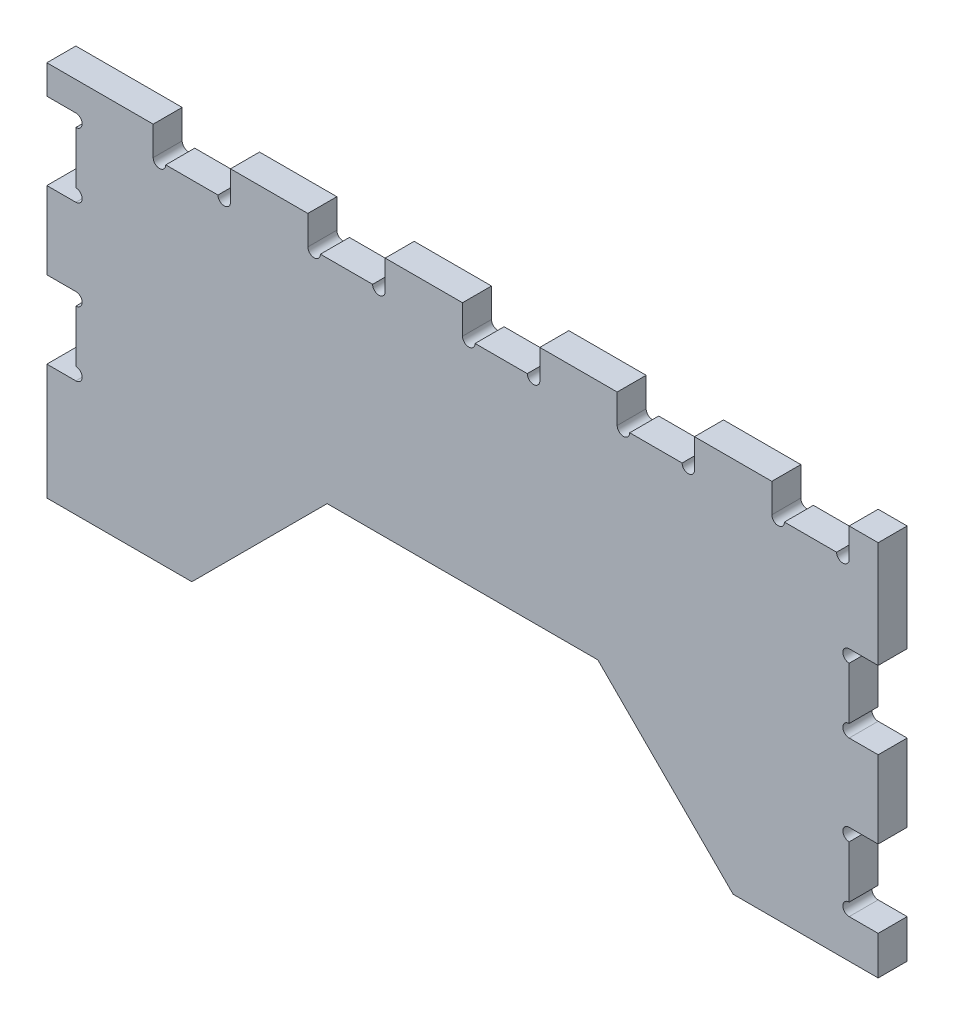
SolidWorks part; units mm, degrees
ref_plane "Alzado" through (0, 0, 0) normal (0, 0, 1) x (1, 0, 0)
ref_plane "Planta" through (0, 0, 0) normal (0, 1, 0) x (1, 0, 0)
ref_plane "Vista lateral" through (0, 0, 0) normal (1, 0, 0) x (0, 0, -1)
sketch "Croquis1" plane through (0, 0, 0) normal (0, 0, 1) x (1, 0, 0)
  line L0 (140, -90) -> (215, -90)
  line L1 (-215, 90) -> (215, 90)
  line L2 (-215, 90) -> (-215, -90)
  line L3 (-215, -90) -> (-140, -90)
  line L4 (215, 90) -> (215, -90)
  line L5 (-215, 90) -> (215, -90) construction
  line L6 (-215, -90) -> (215, 90) construction
  line L7 (140, -90) -> (215, -90)
  line L8 (-215, -90) -> (-140, -90)
  line L9 (-215, -90) -> (-215, -20)
  line L10 (-70, -20) -> (70, -20)
  line L11 (215, -90) -> (215, -20)
  line L12 (-215, -90) -> (-95, -90)
  line L13 (-215, -90) -> (-215, -20)
  line L14 (-215, -20) -> (-95, -20)
  line L17 (215, -90) -> (140, -90)
  line L18 (215, -90) -> (215, -20)
  line L19 (-95, -45) -> (-70, -20)
  line L20 (95, -45) -> (70, -20)
  line L21 (70, -20) -> (140, -90)
  line L22 (-70, -20) -> (-140, -90)
  point P0 (0, 0)
  dimension "D1" = 430
  dimension "D2" = 70
  dimension "75" = 180
  dimension "D3" = 120
extrude "Saliente-Extruir1" add sketch "Croquis1" along normal blind 15
sketch "Croquis2" plane through (0, 90, 0) normal (0, 1, 0) x (1, 0, 0)
  line L4 (215, 0) -> (-215, 0)
  line L5 (-215, 0) -> (-215, -15)
  line L6 (-215, -15) -> (215, -15)
  line L7 (215, -15) -> (215, 0)
  line L8 (215, 0) -> (-215, 0)
  line L9 (-215, 0) -> (-215, -15)
  line L10 (-215, -15) -> (215, -15)
  line L11 (215, -15) -> (215, 0)
  dimension "D1" = 0
extrude "Saliente-Extruir2" add sketch "Croquis2" along normal blind 15
sketch "Croquis3" plane through (0, 0, 15) normal (0, 0, 1) x (1, 0, 0)
  line L0 (0, 105) -> (0, 90)
  line L1 (0, -20) -> (0, 55.1066)
  line L3 (-215, 105) -> (-215, 90)
  line L5 (0, 105) -> (0, 90)
  line L7 (215, 105) -> (215, 90)
  line L8 (-140, -90) -> (-70, -20)
  line L9 (-70, -20) -> (70, -20)
  line L10 (70, -20) -> (140, -90)
  line L11 (140, -90) -> (215, -90)
  line L12 (215, -90) -> (215, 105)
  line L13 (215, 105) -> (-215, 105)
  line L14 (-215, 105) -> (-215, -90)
  line L15 (-215, -90) -> (-140, -90)
  line L17 (-70, -20) -> (70, -20)
  line L18 (70, -20) -> (140, -90)
  line L19 (140, -90) -> (215, -90)
  line L20 (215, -90) -> (215, 105)
  line L22 (-215, 105) -> (-215, -90)
  line L23 (-215, -90) -> (-140, -90)
  line L24 (193.5, 90) -> (166.5, 90)
  line L25 (0, 105) -> (0, 90)
  line L26 (193.5, 90) -> (166.5, 90)
  line L27 (0, 90) -> (0, 140.4543)
  line L30 (200, 90) -> (200, 124.6542)
  line L31 (40, 124.6542) -> (40, 90)
  line L35 (-160, 90) -> (-160, 105)
  line L36 (-160, 124.6542) -> (-120, 124.6542)
  line L37 (-160, 124.6542) -> (-160, 90)
  line L38 (-153.5, 90) -> (-126.5, 90)
  line L39 (-120, 124.6542) -> (-120, 90)
  line L41 (-120, 124.6542) -> (-120, 90)
  line L43 (-80, 124.6542) -> (-80, 90)
  line L44 (-73.5, 90) -> (-46.5, 90)
  line L45 (-80, 90) -> (-80, 124.6542)
  line L46 (-80, 124.6542) -> (-40, 124.6542)
  line L47 (-40, 90) -> (-40, 124.6542)
  line L48 (0, 124.6542) -> (40, 124.6542)
  line L49 (-40, 124.6542) -> (-40, 90)
  line L50 (6.5, 90) -> (33.5, 90)
  line L51 (0, 124.6542) -> (0, 90)
  line L52 (-153.5, 90) -> (-126.5, 90)
  line L53 (40, 90) -> (40, 124.6542)
  line L54 (113.6, 90) -> (86.5, 90)
  line L55 (80, 90) -> (80, 124.6542)
  line L56 (113.6, 90) -> (86.5, 90)
  line L57 (80, 124.6542) -> (80, 90)
  line L58 (120, 124.6542) -> (80, 124.6542)
  line L59 (120, 124.6542) -> (120, 90)
  line L60 (193.5, 90) -> (166.5, 90)
  line L61 (120, 124.6542) -> (120, 90)
  line L62 (-200, 105) -> (-215, 105)
  line L63 (160, 124.6542) -> (160, 90)
  line L64 (200, 124.6542) -> (160, 124.6542)
  line L65 (160, 90) -> (160, 124.6542)
  line L67 (200, 90) -> (200, 124.6542)
  line L76 (113.6, 90) -> (86.5, 90)
  line L82 (-126.5, 90) -> (-153.5, 90)
  line L83 (-73.5, 90) -> (-46.5, 90)
  line L85 (-46.5, 90) -> (-73.5, 90)
  line L89 (33.5, 90) -> (6.5, 90)
  line L90 (33.5, 90) -> (6.5, 90)
  arc A0 (-160, 90) -> (-153.5, 90) centre (-156.75, 90) ccw
  arc A1 (-126.5, 90) -> (-120, 90) centre (-123.25, 90) ccw
  arc A2 (-80, 90) -> (-73.5, 90) centre (-76.75, 90) ccw
  arc A3 (-46.5, 90) -> (-40, 90) centre (-43.25, 90) ccw
  arc A4 (0, 90) -> (6.5, 90) centre (3.25, 90) ccw
  arc A5 (33.5, 90) -> (40, 90) centre (36.75, 90) ccw
  arc A6 (80, 90) -> (86.5, 90) centre (83.25, 90) ccw
  arc A7 (113.6, 90) -> (120, 90) centre (116.8, 90) ccw
  arc A8 (160, 90) -> (166.5, 90) centre (163.25, 90) ccw
  arc A9 (193.5, 90) -> (200, 90) centre (196.75, 90) ccw
  line M48 (215, 105) -> (-215, 105)
  dimension "D2" = 15
  dimension "D3" = 3.25
  dimension "D4" = 3.25
  dimension "D5" = 40
  dimension "D6" = 40
  dimension "D7" = 40
  dimension "D8" = 3.25
  dimension "D9" = 3.25
  dimension "D10" = 3.25
  dimension "D11" = 3.25
  dimension "D12" = 3.25
  dimension "D13" = 3.2
  dimension "D14" = 3.25
  dimension "D15" = 3.25
  dimension "D1" = 0
extrude "Cortar-Extruir2" cut sketch "Croquis3" against normal blind 15 contours L39 L36 L37 M48 | L38 A1 L39 L35 A0 M48 | L44 A3 L47 L43 A2 M48 | L47 L46 L43 M48 | L50 A5 L31 L0 A4 M48 | L48 L27 L31 M48 | L24 A9 L30 L63 A8 M48 | L30 L64 L63 M48 | L59 L58 L55 M48 | L54 A7 L59 L55 A6 M48
sketch "Croquis4" plane through (0, 0, 15) normal (0, 0, 1) x (1, 0, 0)
  line L0 (-215, 10) -> (-215, -90)
  line L2 (-215, 105) -> (-215, 50)
  line L3 (-215, -90) -> (-200, -90)
  line L4 (-200, 83.5) -> (-200, 56.5)
  line L6 (-215, 105) -> (-215, 90)
  line L7 (-215, 90) -> (-200, 90)
  line L9 (-215, 90) -> (-200, 90)
  line L10 (-215, 90) -> (-215, 50)
  line L11 (-215, 50) -> (-200, 50)
  line L12 (-200, 83.5) -> (-200, 56.5)
  line L13 (-215, 50) -> (-200, 50)
  line L15 (-215, 10) -> (-200, 10)
  line L17 (-215, 10) -> (-200, 10)
  line L18 (-215, 10) -> (-215, -30)
  line L19 (-215, -30) -> (-200, -30)
  line L21 (-200, 50) -> (-200, 53.25)
  line L24 (-200, 53.25) -> (-200, 50)
  line L25 (-200, 53.25) -> (-200, 50)
  line L26 (-200, 3.5) -> (-200, -23.5)
  line L27 (-200, 3.5) -> (-200, -23.5)
  line L28 (-80, 105) -> (-120, 105)
  line L29 (-120, 105) -> (-120, 90)
  line L30 (-126.5, 90) -> (-153.5, 90)
  line L31 (-160, 90) -> (-160, 105)
  line L32 (-160, 105) -> (-215, 105)
  line L33 (-215, 105) -> (-215, -90)
  line L34 (-215, -90) -> (-140, -90)
  line L35 (-140, -90) -> (-70, -20)
  line L36 (-70, -20) -> (70, -20)
  line L37 (70, -20) -> (140, -90)
  line L38 (140, -90) -> (215, -90)
  line L39 (215, -90) -> (215, 105)
  line L40 (215, 105) -> (200, 105)
  line L41 (200, 105) -> (200, 90)
  line L42 (193.5, 90) -> (166.5, 90)
  line L43 (160, 90) -> (160, 105)
  line L44 (160, 105) -> (120, 105)
  line L45 (120, 105) -> (120, 90)
  line L46 (113.6, 90) -> (86.5, 90)
  line L47 (80, 90) -> (80, 105)
  line L48 (80, 105) -> (40, 105)
  line L49 (40, 105) -> (40, 90)
  line L50 (33.5, 90) -> (6.5, 90)
  line L51 (0, 90) -> (0, 105)
  line L52 (0, 105) -> (-40, 105)
  line L53 (-40, 105) -> (-40, 90)
  line L54 (-46.5, 90) -> (-73.5, 90)
  line L55 (-80, 90) -> (-80, 105)
  line L56 (-80, 105) -> (-120, 105)
  line L57 (-120, 105) -> (-120, 90)
  line L58 (-126.5, 90) -> (-153.5, 90)
  line L59 (-160, 90) -> (-160, 105)
  line L61 (-215, 105) -> (-215, -90)
  line L62 (-215, -90) -> (-140, -90)
  line L63 (-140, -90) -> (-70, -20)
  line L64 (-70, -20) -> (70, -20)
  line L65 (70, -20) -> (140, -90)
  line L66 (140, -90) -> (215, -90)
  line L67 (215, -90) -> (215, 105)
  line L68 (215, 105) -> (200, 105)
  line L69 (200, 105) -> (200, 90)
  line L70 (193.5, 90) -> (166.5, 90)
  line L71 (160, 90) -> (160, 105)
  line L72 (160, 105) -> (120, 105)
  line L73 (120, 105) -> (120, 90)
  line L74 (113.6, 90) -> (86.5, 90)
  line L75 (80, 90) -> (80, 105)
  line L76 (80, 105) -> (40, 105)
  line L77 (40, 105) -> (40, 90)
  line L78 (33.5, 90) -> (6.5, 90)
  line L79 (0, 90) -> (0, 105)
  line L80 (0, 105) -> (-40, 105)
  line L81 (-40, 105) -> (-40, 90)
  line L82 (-46.5, 90) -> (-73.5, 90)
  line L83 (-80, 90) -> (-80, 105)
  arc A0 (-200, 83.5) -> (-200, 90) centre (-200, 86.75) ccw
  arc A1 (-200, 50) -> (-200, 56.5) centre (-200, 53.25) ccw
  arc A2 (-200, 3.5) -> (-200, 10) centre (-200, 6.75) ccw
  arc A3 (-200, -30) -> (-200, -23.5) centre (-200, -26.75) ccw
  arc A10 (-126.5, 90) -> (-120, 90) centre (-123.25, 90) ccw
  arc A11 (-160, 90) -> (-153.5, 90) centre (-156.75, 90) ccw
  arc A12 (193.5, 90) -> (200, 90) centre (196.75, 90) ccw
  arc A13 (160, 90) -> (166.5, 90) centre (163.25, 90) ccw
  arc A14 (113.6, 90) -> (120, 90) centre (116.8, 90) ccw
  arc A15 (80, 90) -> (86.5, 90) centre (83.25, 90) ccw
  arc A16 (33.5, 90) -> (40, 90) centre (36.75, 90) ccw
  arc A17 (0, 90) -> (6.5, 90) centre (3.25, 90) ccw
  arc A18 (-46.5, 90) -> (-40, 90) centre (-43.25, 90) ccw
  arc A19 (-80, 90) -> (-73.5, 90) centre (-76.75, 90) ccw
  arc A20 (-126.5, 90) -> (-120, 90) centre (-123.25, 90) ccw
  arc A21 (-160, 90) -> (-153.5, 90) centre (-156.75, 90) ccw
  arc A22 (193.5, 90) -> (200, 90) centre (196.75, 90) ccw
  arc A23 (160, 90) -> (166.5, 90) centre (163.25, 90) ccw
  arc A24 (113.6, 90) -> (120, 90) centre (116.8, 90) ccw
  arc A25 (80, 90) -> (86.5, 90) centre (83.25, 90) ccw
  arc A26 (33.5, 90) -> (40, 90) centre (36.75, 90) ccw
  arc A27 (0, 90) -> (6.5, 90) centre (3.25, 90) ccw
  arc A28 (-46.5, 90) -> (-40, 90) centre (-43.25, 90) ccw
  arc A29 (-80, 90) -> (-73.5, 90) centre (-76.75, 90) ccw
  dimension "D3" = 195
  dimension "D4" = 40
  dimension "D5" = 40
  dimension "D6" = 40
  dimension "D7" = 3.25
  dimension "D8" = 3.25
  dimension "D9" = 3.25
  dimension "D10" = 3.25
  dimension "D1" = 0
extrude "Cortar-Extruir3" cut sketch "Croquis4" against normal blind 15
sketch "Croquis5" plane through (0, 0, 15) normal (0, 0, 1) x (1, 0, 0)
  line L2 (215, 105) -> (215, 90)
  line L4 (200, 105) -> (200, 90)
  line L5 (215, -90) -> (200, -90)
  line L6 (215, -70) -> (215, -30)
  line L11 (215, 50) -> (200, 50)
  line L13 (200, 50) -> (215, 50)
  line L15 (200, 10) -> (215, 10)
  line L16 (215, 50) -> (215, 10)
  line L17 (215, 10) -> (200, 10)
  line L19 (215, -30) -> (200, -30)
  line L21 (200, -30) -> (215, -30)
  line L22 (200, -36.5) -> (200, -63.5)
  line L23 (200, -70) -> (215, -70)
  line L24 (215, -30) -> (215, -70)
  line L28 (215, 90) -> (215, 105)
  line L30 (200, 43.5) -> (200, 16.5)
  line L31 (200, 16.5) -> (200, 43.5)
  line L33 (215, 10) -> (215, 50)
  line L34 (215, 10) -> (215, 50)
  line L36 (-200, 50) -> (-215, 50)
  line L37 (-215, 50) -> (-215, 10)
  line L38 (-215, 10) -> (-200, 10)
  line L39 (-200, 3.5) -> (-200, -23.5)
  line L40 (-200, -30) -> (-215, -30)
  line L41 (-215, -30) -> (-215, -90)
  line L42 (-215, -90) -> (-140, -90)
  line L43 (-140, -90) -> (-70, -20)
  line L44 (-70, -20) -> (70, -20)
  line L45 (70, -20) -> (140, -90)
  line L46 (140, -90) -> (215, -90)
  line L47 (215, -90) -> (215, 105)
  line L48 (215, 105) -> (200, 105)
  line L49 (200, 105) -> (200, 90)
  line L50 (193.5, 90) -> (166.5, 90)
  line L51 (160, 90) -> (160, 105)
  line L52 (160, 105) -> (120, 105)
  line L53 (120, 105) -> (120, 90)
  line L54 (113.6, 90) -> (86.5, 90)
  line L55 (80, 90) -> (80, 105)
  line L56 (80, 105) -> (40, 105)
  line L57 (40, 105) -> (40, 90)
  line L58 (33.5, 90) -> (6.5, 90)
  line L59 (0, 90) -> (0, 105)
  line L60 (0, 105) -> (-40, 105)
  line L61 (-40, 105) -> (-40, 90)
  line L62 (-46.5, 90) -> (-73.5, 90)
  line L63 (-80, 90) -> (-80, 105)
  line L64 (-80, 105) -> (-120, 105)
  line L65 (-120, 105) -> (-120, 90)
  line L66 (-126.5, 90) -> (-153.5, 90)
  line L67 (-160, 90) -> (-160, 105)
  line L68 (-160, 105) -> (-215, 105)
  line L69 (-215, 105) -> (-215, 90)
  line L70 (-215, 90) -> (-200, 90)
  line L71 (-200, 83.5) -> (-200, 56.5)
  line L72 (-200, 50) -> (-215, 50)
  line L73 (-215, 50) -> (-215, 10)
  line L74 (-215, 10) -> (-200, 10)
  line L75 (-200, 3.5) -> (-200, -23.5)
  line L76 (-200, -30) -> (-215, -30)
  line L77 (-215, -30) -> (-215, -90)
  line L78 (-215, -90) -> (-140, -90)
  line L79 (-140, -90) -> (-70, -20)
  line L80 (-70, -20) -> (70, -20)
  line L81 (70, -20) -> (140, -90)
  line L82 (140, -90) -> (215, -90)
  line L83 (215, -70) -> (215, -30)
  line L84 (215, 105) -> (200, 105)
  line L85 (200, 105) -> (200, 90)
  line L86 (193.5, 90) -> (166.5, 90)
  line L87 (160, 90) -> (160, 105)
  line L88 (160, 105) -> (120, 105)
  line L89 (120, 105) -> (120, 90)
  line L90 (113.6, 90) -> (86.5, 90)
  line L91 (80, 90) -> (80, 105)
  line L92 (80, 105) -> (40, 105)
  line L93 (40, 105) -> (40, 90)
  line L94 (33.5, 90) -> (6.5, 90)
  line L95 (0, 90) -> (0, 105)
  line L96 (0, 105) -> (-40, 105)
  line L97 (-40, 105) -> (-40, 90)
  line L98 (-46.5, 90) -> (-73.5, 90)
  line L99 (-80, 90) -> (-80, 105)
  line L100 (-80, 105) -> (-120, 105)
  line L101 (-120, 105) -> (-120, 90)
  line L102 (-126.5, 90) -> (-153.5, 90)
  line L103 (-160, 90) -> (-160, 105)
  line L104 (-160, 105) -> (-215, 105)
  line L105 (-215, 105) -> (-215, 90)
  line L106 (-215, 90) -> (-200, 90)
  line L107 (-200, 83.5) -> (-200, 56.5)
  line L108 (200, -63.5) -> (200, -36.5)
  arc A0 (200, 50) -> (200, 43.5) centre (200, 46.75) ccw
  arc A1 (200, 16.5) -> (200, 10) centre (200, 13.25) ccw
  arc A2 (200, -30) -> (200, -36.5) centre (200, -33.25) ccw
  arc A3 (200, -63.5) -> (200, -70) centre (200, -66.75) ccw
  arc A14 (-200, 3.5) -> (-200, 10) centre (-200, 6.75) ccw
  arc A15 (-200, -30) -> (-200, -23.5) centre (-200, -26.75) ccw
  arc A16 (193.5, 90) -> (200, 90) centre (196.75, 90) ccw
  arc A17 (160, 90) -> (166.5, 90) centre (163.25, 90) ccw
  arc A18 (113.6, 90) -> (120, 90) centre (116.8, 90) ccw
  arc A19 (80, 90) -> (86.5, 90) centre (83.25, 90) ccw
  arc A20 (33.5, 90) -> (40, 90) centre (36.75, 90) ccw
  arc A21 (0, 90) -> (6.5, 90) centre (3.25, 90) ccw
  arc A22 (-46.5, 90) -> (-40, 90) centre (-43.25, 90) ccw
  arc A23 (-80, 90) -> (-73.5, 90) centre (-76.75, 90) ccw
  arc A24 (-126.5, 90) -> (-120, 90) centre (-123.25, 90) ccw
  arc A25 (-160, 90) -> (-153.5, 90) centre (-156.75, 90) ccw
  arc A26 (-200, 83.5) -> (-200, 90) centre (-200, 86.75) ccw
  arc A27 (-200, 50) -> (-200, 56.5) centre (-200, 53.25) ccw
  arc A28 (-200, 3.5) -> (-200, 10) centre (-200, 6.75) ccw
  arc A29 (-200, -30) -> (-200, -23.5) centre (-200, -26.75) ccw
  arc A30 (193.5, 90) -> (200, 90) centre (196.75, 90) ccw
  arc A31 (160, 90) -> (166.5, 90) centre (163.25, 90) ccw
  arc A32 (113.6, 90) -> (120, 90) centre (116.8, 90) ccw
  arc A33 (80, 90) -> (86.5, 90) centre (83.25, 90) ccw
  arc A34 (33.5, 90) -> (40, 90) centre (36.75, 90) ccw
  arc A35 (0, 90) -> (6.5, 90) centre (3.25, 90) ccw
  arc A36 (-46.5, 90) -> (-40, 90) centre (-43.25, 90) ccw
  arc A37 (-80, 90) -> (-73.5, 90) centre (-76.75, 90) ccw
  arc A38 (-126.5, 90) -> (-120, 90) centre (-123.25, 90) ccw
  arc A39 (-160, 90) -> (-153.5, 90) centre (-156.75, 90) ccw
  arc A40 (-200, 83.5) -> (-200, 90) centre (-200, 86.75) ccw
  arc A41 (-200, 50) -> (-200, 56.5) centre (-200, 53.25) ccw
  line M91 (215, -90) -> (215, 105)
  dimension "D2" = 40
  dimension "D3" = 40
  dimension "D4" = 40
  dimension "D5" = 40
  dimension "D6" = 3.25
  dimension "D7" = 3.25
  dimension "D8" = 3.25
  dimension "D9" = 3.25
  dimension "D1" = 0
extrude "Cortar-Extruir4" cut sketch "Croquis5" against normal blind 15 contours L30 A1 L15 L11 A0 M91 | L22 A3 L23 L19 A2 M91
sketch "Croquis6" plane through (0, 0, 15) normal (0, 0, 1) x (1, 0, 0)
  line L0 (-160, 105) -> (-160, 90) construction
